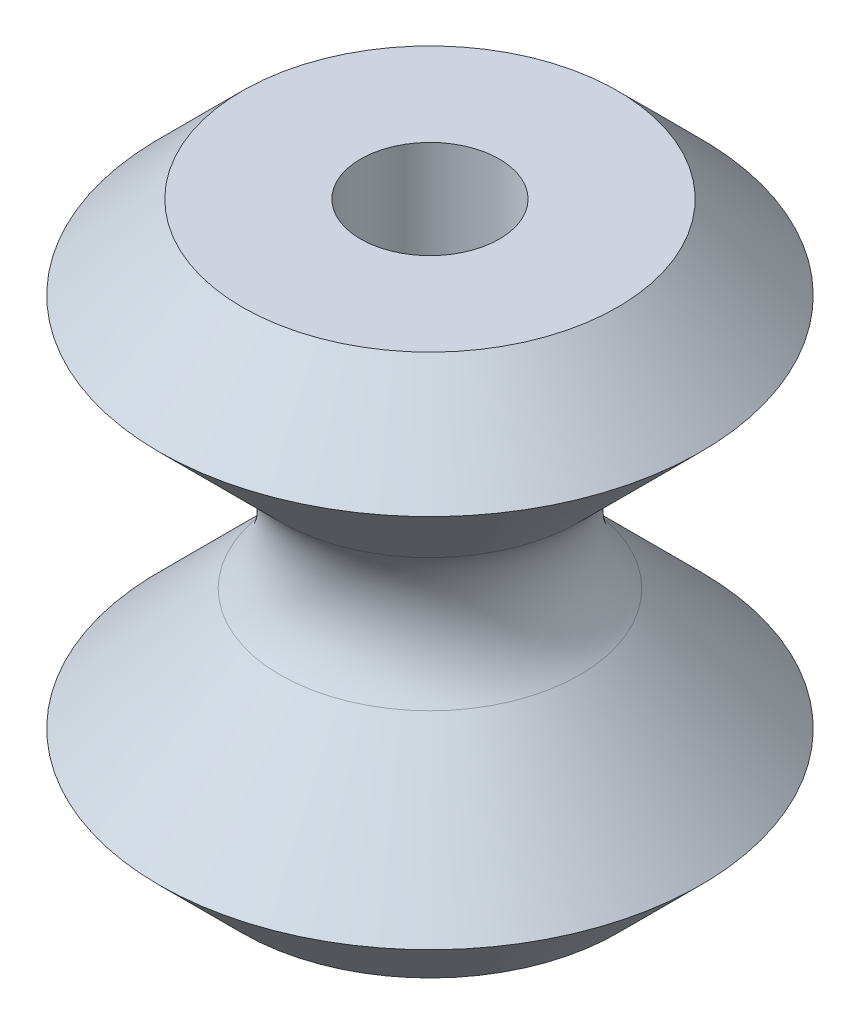
SolidWorks part; units mm, degrees
ref_plane "Front Plane" through (0, 0, 0) normal (0, 0, 1) x (1, 0, 0)
ref_plane "Top Plane" through (0, 0, 0) normal (0, 1, 0) x (1, 0, 0)
ref_plane "Right Plane" through (0, 0, 0) normal (1, 0, 0) x (0, 0, -1)
sketch "Sketch2" plane through (0, 0, 0) normal (0, 0, 1) x (1, 0, 0)
  line L0 (9.1758, 2.8257) -> (6.35, 0)
  line L1 (9.1758, 2.8257) -> (2.8257, 9.1757)
  line L2 (2.8257, 9.1757) -> (9.1758, 15.5257)
  line L3 (6.35, 0) -> (0, 0)
  line L4 (0, 18.3515) -> (0, 0)
  line L5 (0, 18.3515) -> (6.35, 18.3515)
  line L6 (6.35, 18.3515) -> (9.1758, 15.5257)
  line L7 (9.1758, 15.5257) -> (9.1758, 2.8257) construction
  point P4 (0, 9.1757)
  dimension "D1" = 6.35
  dimension "D2" = 18.3515
  dimension "D3" = 6.35
revolve "Revolve1" add sketch "Sketch2" angle 360 about L4
sketch "Sketch3" plane through (0, 18.3515, 0) normal (0, 1, 0) x (1, 0, 0)
  circle A0 centre (0, 0) radius 2.3495
  dimension "D1" = 4.699
extrude "Cut-Extrude1" cut sketch "Sketch3" against normal through all
fillet "Fillet1" radius 3.175 1 edges at (0, 9.1757, 2.8257)
